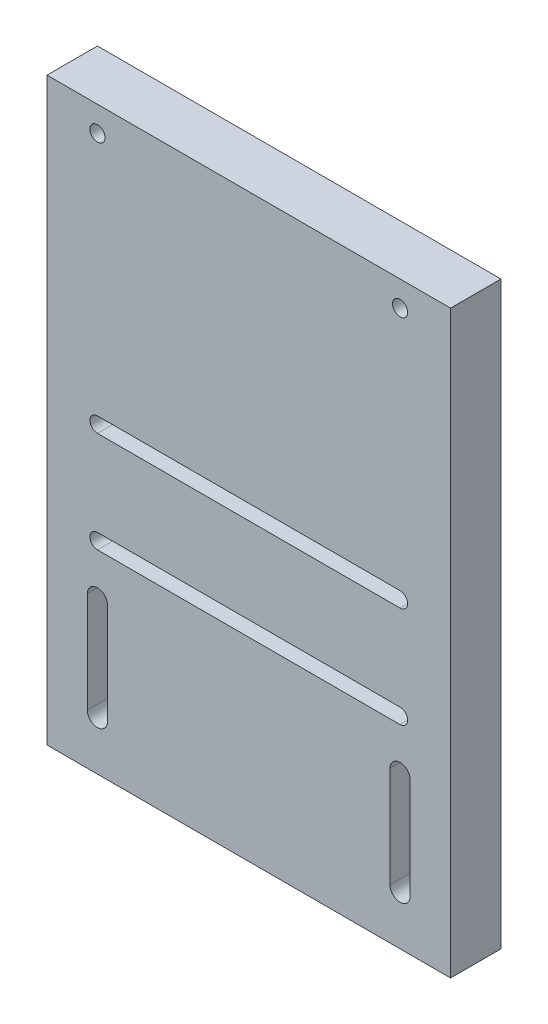
SolidWorks part; units mm, degrees
material "Pin"
ref_plane "Plan de face" through (0, 0, 0) normal (0, 0, 1) x (1, 0, 0)
ref_plane "Plan de dessus" through (0, 0, 0) normal (0, 1, 0) x (1, 0, 0)
ref_plane "Plan de droite" through (0, 0, 0) normal (1, 0, 0) x (0, 0, -1)
sketch "Esquisse1" plane through (0, 0, 0) normal (0, 0, 1) x (1, 0, 0)
  line L0 (-47.728, 28.7016) -> (12.272, 28.7016)
  line L1 (-57.728, 82.2016) -> (22.272, 82.2016)
  line L2 (-57.728, 82.2016) -> (-57.728, -32.7984)
  line L3 (-57.728, -32.7984) -> (22.272, -32.7984)
  line L4 (22.272, 82.2016) -> (22.272, -32.7984)
  line L5 (-47.728, 25.7016) -> (12.272, 25.7016)
  line L6 (-57.728, 27.2016) -> (-47.728, 27.2016) construction
  line L7 (-47.728, 27.2016) -> (12.272, 27.2016) construction
  line L8 (12.272, 27.2016) -> (22.272, 27.2016) construction
  line L9 (-47.728, 82.2016) -> (-47.728, 27.2016) construction
  line L10 (-47.728, 27.2016) -> (-47.728, 7.2016) construction
  line L11 (-47.728, 7.2016) -> (-47.728, -32.7984) construction
  line L12 (-57.728, 7.2016) -> (-47.728, 7.2016) construction
  line L13 (-47.728, 7.2016) -> (12.272, 7.2016) construction
  line L14 (12.272, 7.2016) -> (22.272, 7.2016) construction
  line L15 (12.272, 82.2016) -> (12.272, 27.2016) construction
  line L16 (12.272, 27.2016) -> (12.272, 7.2016) construction
  line L17 (12.272, 7.2016) -> (12.272, -32.7984) construction
  line L18 (-47.728, 8.7016) -> (12.272, 8.7016)
  line L19 (12.272, 5.7016) -> (-47.728, 5.7016)
  line L20 (-47.728, 77.2016) -> (-57.728, 77.2016) construction
  line L21 (-47.728, 77.2016) -> (12.272, 77.2016) construction
  line L22 (12.272, 77.2016) -> (22.272, 77.2016) construction
  line L23 (-57.728, -2.7984) -> (-47.728, -2.7984) construction
  line L24 (-47.728, -2.7984) -> (12.272, -2.7984) construction
  line L25 (12.272, -2.7984) -> (22.272, -2.7984) construction
  line L26 (-57.728, -22.7984) -> (-47.728, -22.7984) construction
  line L27 (-47.728, -22.7984) -> (12.272, -22.7984) construction
  line L28 (12.272, -22.7984) -> (22.272, -22.7984) construction
  line L29 (-49.728, -22.7984) -> (-49.728, -2.7984)
  line L30 (-45.728, -2.7984) -> (-45.728, -22.7984)
  line L31 (10.272, -2.7984) -> (10.272, -22.7984)
  line L32 (14.272, -22.7984) -> (14.272, -2.7984)
  arc A0 (-47.728, 28.7016) -> (-47.728, 25.7016) centre (-47.728, 27.2016) ccw
  arc A1 (12.272, 28.7016) -> (12.272, 25.7016) centre (12.272, 27.2016) cw
  arc A2 (-47.728, 8.7016) -> (-47.728, 5.7016) centre (-47.728, 7.2016) ccw
  arc A3 (12.272, 8.7016) -> (12.272, 5.7016) centre (12.272, 7.2016) cw
  circle A4 centre (-47.728, 77.2016) radius 1.5
  circle A5 centre (12.272, 77.2016) radius 1.5
  arc A6 (-49.728, -2.7984) -> (-45.728, -2.7984) centre (-47.728, -2.7984) cw
  arc A7 (-49.728, -22.7984) -> (-45.728, -22.7984) centre (-47.728, -22.7984) ccw
  arc A8 (10.272, -2.7984) -> (14.272, -2.7984) centre (12.272, -2.7984) cw
  arc A9 (10.272, -22.7984) -> (14.272, -22.7984) centre (12.272, -22.7984) ccw
  dimension "D3" = 55
  dimension "D6" = 1.5
  dimension "D7" = 3
  dimension "D9" = 10
  dimension "D10" = 2
  dimension "D1" = 80
  dimension "D2" = 115
  dimension "D4" = 10
  dimension "D5" = 20
  dimension "D8" = 5
  dimension "D11" = 10
extrude "Boss.-Extru.1" add sketch "Esquisse1" along normal blind 10
ref_plane "Plan1" through (-49.728, -22.7984, 0) normal (0, -1, 0) x (-1, 0, 0)
